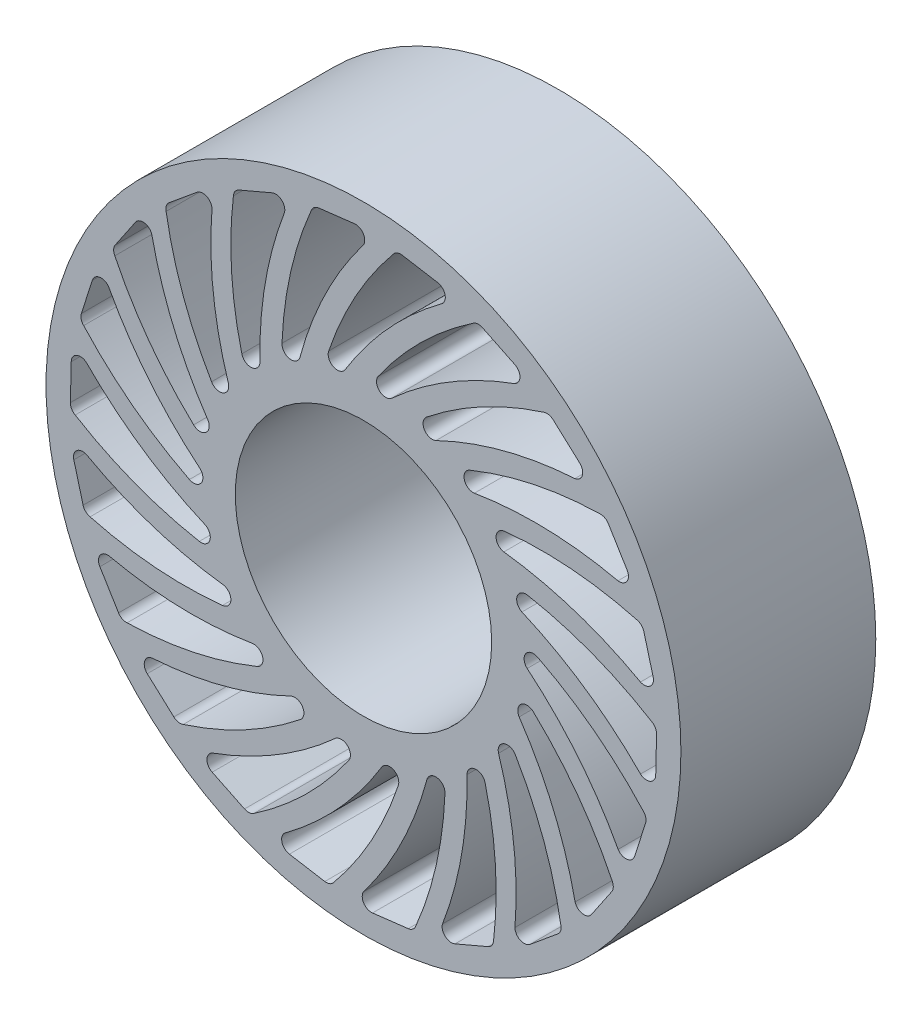
SolidWorks part; units mm, degrees
material "Rubber"
ref_plane "Front" through (0, 0, 0) normal (0, 0, 1) x (1, 0, 0)
ref_plane "Top" through (0, 0, 0) normal (0, 1, 0) x (1, 0, 0)
ref_plane "Right" through (0, 0, 0) normal (1, 0, 0) x (0, 0, -1)
sketch "Sketch1" plane through (0, 0, 0) normal (0, 0, 1) x (1, 0, 0)
  line L2 (11.6337, -75.331) -> (2.3587, -76.4363)
  arc A9 (11.6337, -75.331) -> (13.5911, -73.787) centre (11.3512, -72.9602) ccw
  arc A10 (21.1927, -40.0853) -> (16.5267, -39.2502) centre (18.8089, -39.9518) ccw
  arc A11 (0.0515, -72.7765) -> (2.3587, -76.4363) centre (2.06, -74.0675) ccw
  arc A12 (0.0515, -72.7765) -> (16.5267, -39.2502) centre (-77.2792, -13.9643) ccw
  arc A13 (13.5911, -73.787) -> (21.1927, -40.0853) centre (-73.672, -36.396) ccw
  circle A104 centre (0, 0) radius 82.55
  circle A105 centre (0, 0) radius 33.3375
  dimension "D1" = 165.1
  dimension "D2" = 66.675
extrude "Base-Extrude" add sketch "Sketch1" along normal mid plane 50.673
sketch "Sketch2" plane through (0, 0, 25.3365) normal (0, 0, 1) x (1, 0, 0)
  line L0 (2.3587, -76.4363) -> (11.6337, -75.331) construction
  line L1 (2.3587, -76.4363) -> (11.6337, -75.331)
  line L2 (-19.2714, -74.0046) -> (-10.0607, -75.5572)
  line L3 (-39.3403, -65.5775) -> (-30.9401, -69.6621)
  line L4 (-56.2221, -51.8377) -> (-49.3129, -58.1235)
  line L5 (-68.5491, -33.8983) -> (-63.6907, -41.8761)
  line L6 (-75.3226, -13.2127) -> (-72.9086, -22.2361)
  line L7 (-75.994, 8.5433) -> (-76.2199, -0.7946)
  line L8 (-70.5088, 29.6073) -> (-73.3563, 20.7112)
  line L9 (-59.3113, 48.2726) -> (-64.5499, 40.5391)
  line L10 (-43.3089, 63.0271) -> (-50.5139, 57.0828)
  line L11 (-23.7978, 72.6756) -> (-32.3857, 69.002)
  line L12 (-2.3587, 76.4363) -> (-11.6337, 75.331)
  line L13 (19.2714, 74.0046) -> (10.0607, 75.5572)
  line L14 (39.3403, 65.5775) -> (30.9401, 69.6621)
  line L15 (56.2221, 51.8377) -> (49.3129, 58.1235)
  line L16 (68.5491, 33.8983) -> (63.6907, 41.8761)
  line L17 (75.3226, 13.2127) -> (72.9086, 22.2361)
  line L18 (75.994, -8.5433) -> (76.2199, 0.7946)
  line L19 (70.5088, -29.6073) -> (73.3563, -20.7112)
  line L20 (59.3113, -48.2726) -> (64.5499, -40.5391)
  line L21 (43.3089, -63.0271) -> (50.5139, -57.0828)
  line L22 (23.7978, -72.6756) -> (32.3857, -69.002)
  arc A0 (13.5911, -73.787) -> (21.1927, -40.0853) centre (-73.672, -36.396) ccw construction
  arc A1 (11.6337, -75.331) -> (13.5911, -73.787) centre (11.3512, -72.9602) ccw construction
  arc A2 (0.0515, -72.7765) -> (2.3587, -76.4363) centre (2.06, -74.0675) ccw construction
  arc A3 (0.0515, -72.7765) -> (16.5267, -39.2502) centre (-77.2792, -13.9643) ccw construction
  arc A4 (21.1927, -40.0853) -> (16.5267, -39.2502) centre (18.8089, -39.9518) ccw construction
  arc A5 (13.5911, -73.787) -> (21.1927, -40.0853) centre (-73.672, -36.396) ccw
  arc A6 (11.6337, -75.331) -> (13.5911, -73.787) centre (11.3512, -72.9602) ccw
  arc A7 (0.0515, -72.7765) -> (2.3587, -76.4363) centre (2.06, -74.0675) ccw
  arc A8 (0.0515, -72.7765) -> (16.5267, -39.2502) centre (-77.2792, -13.9643) ccw
  arc A9 (21.1927, -40.0853) -> (16.5267, -39.2502) centre (18.8089, -39.9518) ccw
  arc A10 (-20.4541, -69.8431) -> (4.7992, -42.3164) centre (-78.0831, 8.3734) ccw
  arc A11 (-20.4541, -69.8431) -> (-19.2714, -74.0046) centre (-18.8907, -71.6476) ccw
  arc A12 (-10.0607, -75.5572) -> (-7.7477, -74.6272) centre (-9.6639, -73.2028) ccw
  arc A13 (-7.7477, -74.6272) -> (9.0409, -44.4323) centre (-80.9417, -14.1659) ccw
  arc A14 (9.0409, -44.4323) -> (4.7992, -42.3164) centre (6.7913, -43.6325) ccw
  arc A15 (-39.3026, -61.2514) -> (-7.3171, -41.9543) centre (-72.5611, 30.0328) ccw
  arc A16 (-39.3026, -61.2514) -> (-39.3403, -65.5775) centre (-38.3109, -63.4233) ccw
  arc A17 (-30.9401, -69.6621) -> (-28.4587, -69.4215) centre (-29.896, -67.5149) ccw
  arc A18 (-28.4587, -69.4215) -> (-3.8433, -45.1796) centre (-81.654, 9.2118) ccw
  arc A19 (-3.8433, -45.1796) -> (-7.3171, -41.9543) centre (-5.7765, -43.7784) ccw
  arc A20 (-54.9671, -47.6974) -> (-18.8406, -38.1934) centre (-61.1606, 49.2591) ccw
  arc A21 (-54.9671, -47.6974) -> (-56.2221, -51.8377) centre (-54.6275, -50.0607) ccw
  arc A22 (-49.3129, -58.1235) -> (-46.8642, -58.5917) centre (-47.7062, -56.3574) ccw
  arc A23 (-46.8642, -58.5917) -> (-16.4162, -42.2667) centre (-75.7512, 31.8433) ccw
  arc A24 (-16.4162, -42.2667) -> (-18.8406, -38.1934) centre (-17.8763, -40.3777) ccw
  arc A25 (-66.1784, -30.2793) -> (-28.8378, -31.3383) centre (-44.8053, 64.4947) ccw
  arc A26 (-66.1784, -30.2793) -> (-68.5491, -33.8983) centre (-66.5184, -32.6426) ccw
  arc A27 (-63.6907, -41.8761) -> (-61.4731, -43.0151) centre (-61.6515, -40.6342) ccw
  arc A28 (-61.4731, -43.0151) -> (-27.6591, -35.9296) centre (-63.7114, 51.895) ccw
  arc A29 (-27.6591, -35.9296) -> (-28.8378, -31.3383) centre (-28.5279, -33.7057) ccw
  arc A30 (-72.0284, -10.4082) -> (-36.4987, -21.9444) centre (-24.8201, 74.5053) ccw
  arc A31 (-72.0284, -10.4082) -> (-75.3226, -13.2127) centre (-73.0204, -12.58) ccw
  arc A32 (-72.9086, -22.2361) -> (-71.1017, -23.9537) centre (-70.6021, -21.619) ccw
  arc A33 (-71.1017, -23.9537) -> (-36.6613, -26.6818) centre (-46.5102, 67.7424) ccw
  arc A34 (-36.6613, -26.6818) -> (-36.4987, -21.9444) centre (-36.8683, -24.3032) ccw
  arc A35 (-72.0431, 10.3062) -> (-41.2027, -10.7726) centre (-2.8242, 78.4799) ccw
  arc A36 (-72.0431, 10.3062) -> (-75.994, 8.5433) centre (-73.6068, 8.5019) ccw
  arc A37 (-76.2199, -0.7946) -> (-74.9702, -2.9517) centre (-73.833, -0.8524) ccw
  arc A38 (-74.9702, -2.9517) -> (-42.6934, -15.2723) centre (-25.5409, 78.1018) ccw
  arc A39 (-42.6934, -15.2723) -> (-41.2027, -10.7726) centre (-42.2219, -12.9317) ccw
  arc A40 (-66.2213, 30.1856) -> (-42.5686, 1.2719) centre (19.4006, 76.0966) ccw
  arc A41 (-66.2213, 30.1856) -> (-70.5088, 29.6073) centre (-68.2299, 28.8949) ccw
  arc A42 (-73.3563, 20.7112) -> (-72.7649, 18.2894) centre (-71.0824, 19.9833) ccw
  arc A43 (-72.7649, 18.2894) -> (-45.2667, -2.6255) centre (-2.5025, 82.1339) ccw
  arc A44 (-45.2667, -2.6255) -> (-42.5686, 1.2719) centre (-44.1549, -0.5126) ccw
  arc A45 (-55.0346, 47.6195) -> (-40.486, 13.2134) centre (40.0536, 67.5484) ccw
  arc A46 (-55.0346, 47.6195) -> (-59.3113, 48.2726) centre (-57.3255, 46.947) ccw
  arc A47 (-64.5499, 40.5391) -> (-64.6647, 38.0488) centre (-62.5731, 39.2001) ccw
  arc A48 (-64.6647, 38.0488) -> (-44.1728, 10.2339) centre (20.7386, 79.5119) ccw
  arc A49 (-44.1728, 10.2339) -> (-40.486, 13.2134) centre (-42.5107, 11.948) ccw
  arc A50 (-39.3893, 61.1956) -> (-35.1234, 24.0843) centre (57.4618, 53.5278) ccw
  arc A51 (-39.3893, 61.1956) -> (-43.3089, 63.0271) centre (-41.7769, 61.1958) ccw
  arc A52 (-50.5139, 57.0828) -> (-51.3258, 54.7257) centre (-48.9945, 55.2411) ccw
  arc A53 (-51.3258, 54.7257) -> (-39.5002, 22.2643) centre (42.2997, 70.4484) ccw
  arc A54 (-39.5002, 22.2643) -> (-35.1234, 24.0843) centre (-37.4226, 23.4407) ccw
  arc A55 (-20.553, 69.814) -> (-26.9153, 33.0042) centre (70.2147, 35.1707) ccw
  arc A56 (-20.553, 69.814) -> (-23.7978, 72.6756) centre (-22.8438, 70.4869) ccw
  arc A57 (-32.3857, 69.002) -> (-33.8287, 66.9691) centre (-31.4467, 66.8068) ccw
  arc A58 (-33.8287, 66.9691) -> (-31.6276, 32.4909) centre (60.4338, 55.6775) ccw
  arc A59 (-31.6276, 32.4909) -> (-26.9153, 33.0042) centre (-29.3027, 33.0344) ccw
  arc A60 (-0.0515, 72.7765) -> (-16.5267, 39.2502) centre (77.2792, 13.9643) ccw
  arc A61 (-0.0515, 72.7765) -> (-2.3587, 76.4363) centre (-2.06, 74.0675) ccw
  arc A62 (-11.6337, 75.331) -> (-13.5911, 73.787) centre (-11.3512, 72.9602) ccw
  arc A63 (-13.5911, 73.787) -> (-21.1927, 40.0853) centre (73.672, 36.396) ccw
  arc A64 (-21.1927, 40.0853) -> (-16.5267, 39.2502) centre (-18.8089, 39.9518) ccw
  arc A65 (20.4541, 69.8431) -> (-4.7992, 42.3164) centre (78.0831, -8.3734) ccw
  arc A66 (20.4541, 69.8431) -> (19.2714, 74.0046) centre (18.8907, 71.6476) ccw
  arc A67 (10.0607, 75.5572) -> (7.7477, 74.6272) centre (9.6639, 73.2028) ccw
  arc A68 (7.7477, 74.6272) -> (-9.0409, 44.4323) centre (80.9417, 14.1659) ccw
  arc A69 (-9.0409, 44.4323) -> (-4.7992, 42.3164) centre (-6.7913, 43.6325) ccw
  arc A70 (39.3026, 61.2514) -> (7.3171, 41.9543) centre (72.5611, -30.0328) ccw
  arc A71 (39.3026, 61.2514) -> (39.3403, 65.5775) centre (38.3109, 63.4233) ccw
  arc A72 (30.9401, 69.6621) -> (28.4587, 69.4215) centre (29.896, 67.5149) ccw
  arc A73 (28.4587, 69.4215) -> (3.8433, 45.1796) centre (81.654, -9.2118) ccw
  arc A74 (3.8433, 45.1796) -> (7.3171, 41.9543) centre (5.7765, 43.7784) ccw
  arc A75 (54.9671, 47.6974) -> (18.8406, 38.1934) centre (61.1606, -49.2591) ccw
  arc A76 (54.9671, 47.6974) -> (56.2221, 51.8377) centre (54.6275, 50.0607) ccw
  arc A77 (49.3129, 58.1235) -> (46.8642, 58.5917) centre (47.7062, 56.3574) ccw
  arc A78 (46.8642, 58.5917) -> (16.4162, 42.2667) centre (75.7512, -31.8433) ccw
  arc A79 (16.4162, 42.2667) -> (18.8406, 38.1934) centre (17.8763, 40.3777) ccw
  arc A80 (66.1784, 30.2793) -> (28.8378, 31.3383) centre (44.8053, -64.4947) ccw
  arc A81 (66.1784, 30.2793) -> (68.5491, 33.8983) centre (66.5184, 32.6426) ccw
  arc A82 (63.6907, 41.8761) -> (61.4731, 43.0151) centre (61.6515, 40.6342) ccw
  arc A83 (61.4731, 43.0151) -> (27.6591, 35.9296) centre (63.7114, -51.895) ccw
  arc A84 (27.6591, 35.9296) -> (28.8378, 31.3383) centre (28.5279, 33.7057) ccw
  arc A85 (72.0284, 10.4082) -> (36.4987, 21.9444) centre (24.8201, -74.5053) ccw
  arc A86 (72.0284, 10.4082) -> (75.3226, 13.2127) centre (73.0204, 12.58) ccw
  arc A87 (72.9086, 22.2361) -> (71.1017, 23.9537) centre (70.6021, 21.619) ccw
  arc A88 (71.1017, 23.9537) -> (36.6613, 26.6818) centre (46.5102, -67.7424) ccw
  arc A89 (36.6613, 26.6818) -> (36.4987, 21.9444) centre (36.8683, 24.3032) ccw
  arc A90 (72.0431, -10.3062) -> (41.2027, 10.7726) centre (2.8242, -78.4799) ccw
  arc A91 (72.0431, -10.3062) -> (75.994, -8.5433) centre (73.6068, -8.5019) ccw
  arc A92 (76.2199, 0.7946) -> (74.9702, 2.9517) centre (73.833, 0.8524) ccw
  arc A93 (74.9702, 2.9517) -> (42.6934, 15.2723) centre (25.5409, -78.1018) ccw
  arc A94 (42.6934, 15.2723) -> (41.2027, 10.7726) centre (42.2219, 12.9317) ccw
  arc A95 (66.2213, -30.1856) -> (42.5686, -1.2719) centre (-19.4006, -76.0966) ccw
  arc A96 (66.2213, -30.1856) -> (70.5088, -29.6073) centre (68.2299, -28.8949) ccw
  arc A97 (73.3563, -20.7112) -> (72.7649, -18.2894) centre (71.0824, -19.9833) ccw
  arc A98 (72.7649, -18.2894) -> (45.2667, 2.6255) centre (2.5025, -82.1339) ccw
  arc A99 (45.2667, 2.6255) -> (42.5686, -1.2719) centre (44.1549, 0.5126) ccw
  arc A100 (55.0346, -47.6195) -> (40.486, -13.2134) centre (-40.0536, -67.5484) ccw
  arc A101 (55.0346, -47.6195) -> (59.3113, -48.2726) centre (57.3255, -46.947) ccw
  arc A102 (64.5499, -40.5391) -> (64.6647, -38.0488) centre (62.5731, -39.2001) ccw
  arc A103 (64.6647, -38.0488) -> (44.1728, -10.2339) centre (-20.7386, -79.5119) ccw
  arc A104 (44.1728, -10.2339) -> (40.486, -13.2134) centre (42.5107, -11.948) ccw
  arc A105 (39.3893, -61.1956) -> (35.1234, -24.0843) centre (-57.4618, -53.5278) ccw
  arc A106 (39.3893, -61.1956) -> (43.3089, -63.0271) centre (41.7769, -61.1958) ccw
  arc A107 (50.5139, -57.0828) -> (51.3258, -54.7257) centre (48.9945, -55.2411) ccw
  arc A108 (51.3258, -54.7257) -> (39.5002, -22.2643) centre (-42.2997, -70.4484) ccw
  arc A109 (39.5002, -22.2643) -> (35.1234, -24.0843) centre (37.4226, -23.4407) ccw
  arc A110 (20.553, -69.814) -> (26.9153, -33.0042) centre (-70.2147, -35.1707) ccw
  arc A111 (20.553, -69.814) -> (23.7978, -72.6756) centre (22.8438, -70.4869) ccw
  arc A112 (32.3857, -69.002) -> (33.8287, -66.9691) centre (31.4467, -66.8068) ccw
  arc A113 (33.8287, -66.9691) -> (31.6276, -32.4909) centre (-60.4338, -55.6775) ccw
  arc A114 (31.6276, -32.4909) -> (26.9153, -33.0042) centre (29.3027, -33.0344) ccw
extrude "Cut-Extrude2" cut sketch "Sketch2" against normal through all
ref_plane "Plane1 Downstream Edge " through (-82.55, 0, 0) normal (-1, 0, 0) x (0, 0, 1)
ref_plane "Plane2 BPH" through (0, -82.55, 0) normal (0, -1, 0) x (1, 0, 0)
ref_plane "Plane3 Upstream Edge" through (82.55, 0, 0) normal (1, 0, 0) x (0, 0, -1)
